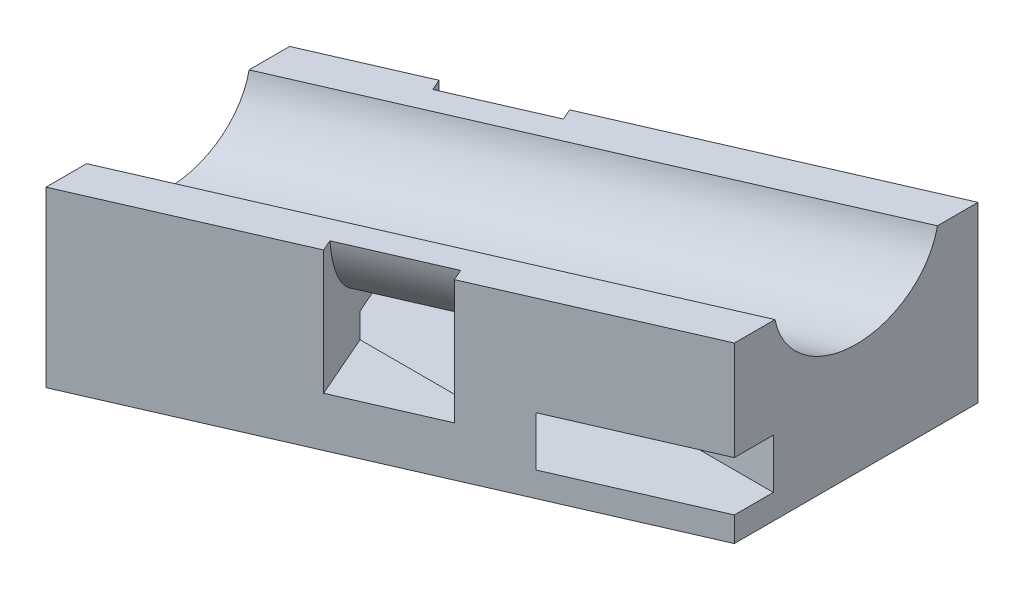
SolidWorks part; units mm, degrees
ref_plane "Front Plane" through (0, 0, 0) normal (0, 0, 1) x (1, 0, 0)
ref_plane "Top Plane" through (0, 0, 0) normal (0, 1, 0) x (1, 0, 0)
ref_plane "Right Plane" through (0, 0, 0) normal (1, 0, 0) x (0, 0, -1)
sketch "Sketch2" plane through (0, 0, 0) normal (0, 1, 0) x (1, 0, 0)
  line L0 (0, 0) -> (-3.6, 8.2486)
  line L1 (-3.6, 8.2486) -> (19.3129, 18.2486)
  line L2 (19.3129, 18.2486) -> (22.9129, 10)
  line L3 (22.9129, 10) -> (0, 0)
  dimension "D1" = 25
  dimension "D2" = 9
  dimension "D3" = 10
extrude "Boss-Extrude2" add sketch "Sketch2" along normal blind 7
sketch "Sketch4" plane through (0, 0, 0) normal (-0.9165, 0, 0.4) x (0.4, 0, 0.9165)
  line L1 (-9, 4.5) -> (0, 4.5) construction
  line L2 (-9, 7) -> (-9, 0) construction
  line L4 (0, 7) -> (0, 0) construction
  line L6 (-9, 7) -> (0, 7) construction
  line L7 (-7.5, 7) -> (-1.5, 7)
  arc A0 (-7.5, 7) -> (-1.5, 7) centre (-4.5, 7.55) ccw
  dimension "D1" = 1.5
  dimension "D2" = 2.5
  dimension "D3" = 1.5
extrude "Cut-Extrude4" cut sketch "Sketch4" against normal up to surface (25 mm away) up to face at (21.1129, 3.5, -14.1243)
ref_plane "Plane1" through (11.4564, 0, -5) normal (0.9165, 0, -0.4) x (-0.4, 0, -0.9165)
sketch "Sketch8" plane through (11.4564, 0, -5) normal (0.9165, 0, -0.4) x (-0.4, 0, -0.9165)
  line L0 (9, 7) -> (9, 0) construction
  line L1 (0, 7) -> (0, 0) construction
  line L2 (0.4875, 7) -> (0, 7)
  line L3 (0, 7) -> (0, 2)
  line L4 (0, 7) -> (1.5, 7) construction
  line L5 (7.5, 7) -> (9, 7) construction
  line L6 (8.5125, 7) -> (9, 7)
  line L7 (9, 7) -> (9, 2)
  line L8 (0, 2) -> (9, 2)
  line L9 (4.5, 3.5) -> (9, 3.5) construction
  arc A0 (8.5125, 7) -> (0.4875, 7) centre (4.5, 7.55) cw
  dimension "D1" = 4.05
  dimension "D2" = 1.5
extrude "Cut-Extrude7" cut sketch "Sketch8" against normal blind 4
sketch "Sketch6" plane through (0, 0, 0) normal (1, 0, 0) x (0, 0, -1)
  line L1 (6, 1) -> (10, 1)
  line L2 (6, 1) -> (6, 3)
  line L3 (6, 3) -> (10, 3)
  line L4 (10, 1) -> (10, 3)
  line L8 (0, 7) -> (0, 0) construction
  line L13 (0, 0) -> (10, 0) construction
  dimension "D1" = 1
  dimension "D2" = 2
  dimension "D3" = 4
  dimension "D4" = 6
extrude "Cut-Extrude5" cut sketch "Sketch6" against normal through all and the other way through all
sketch "Sketch12" plane through (0, 0, 0) normal (0, 1, 0) x (1, 0, 0)
  line L0 (22.9129, 8.4288) -> (22.9129, 18.2486)
  line L1 (22.9129, 18.2486) -> (19.3129, 18.2486)
  line L2 (19.3129, 18.2486) -> (19.3129, 8.4288)
  line L3 (19.3129, 8.4288) -> (22.9129, 8.4288)
  line L4 (22.9129, 10) -> (13.7477, 6) construction
extrude "Cut-Extrude10" cut sketch "Sketch12" along normal through all
sketch "Sketch13" plane through (0, 0, 0) normal (0, 1, 0) x (1, 0, 0)
  line L0 (0, 0) -> (0, 9.8198)
  line L1 (0, 9.8198) -> (-3.6, 9.8198)
  line L2 (-3.6, 9.8198) -> (-3.6, 0)
  line L3 (-3.6, 0) -> (0, 0)
  line L4 (-3.6, 8.2486) -> (0.4129, 10) construction
extrude "Cut-Extrude11" cut sketch "Sketch13" along normal through all
